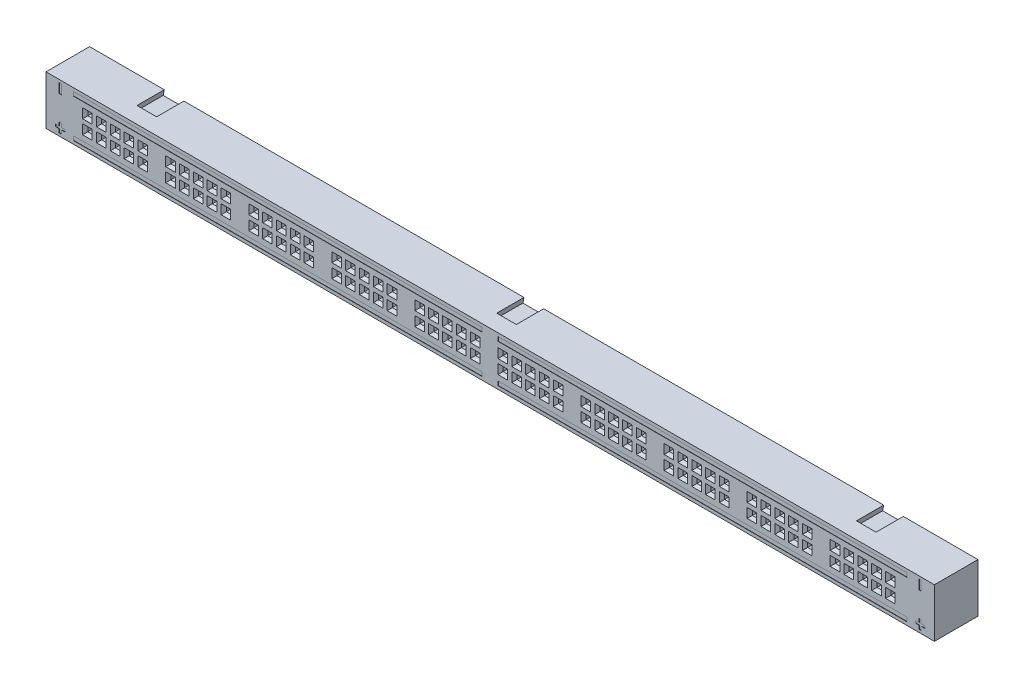
SolidWorks part; units mm, degrees
ref_plane "Front Plane" through (0, 0, 0) normal (0, 0, 1) x (1, 0, 0)
ref_plane "Top Plane" through (0, 0, 0) normal (0, 1, 0) x (1, 0, 0)
ref_plane "Right Plane" through (0, 0, 0) normal (1, 0, 0) x (0, 0, -1)
sketch "Sketch1" plane through (0, 0, 0) normal (0, 0, 1) x (1, 0, 0)
  line L1 (0, 0) -> (163, 0)
  line L2 (0, 0) -> (0, 9)
  line L3 (0, 9) -> (163, 9)
  line L4 (163, 0) -> (163, 9)
  dimension "D1" = 163
  dimension "D2" = 9
extrude "Boss-Extrude1" add sketch "Sketch1" along normal blind 8
sketch "Sketch2" plane through (0, 0, 8) normal (0, 0, 1) x (1, 0, 0)
  line L0 (163, 0) -> (163, 9) construction
  line L1 (163, 0) -> (163, 9)
  line L2 (154.92, 0) -> (154.92, 9) construction
  line L3 (154.92, 4.5) -> (159.3402, 4.5) construction
  line L5 (154.92, 5.77) -> (159.3402, 5.77) construction
  line L6 (154.045, 6.645) -> (155.795, 6.645)
  line L7 (154.045, 6.645) -> (154.045, 4.895)
  line L8 (154.045, 4.895) -> (155.795, 4.895)
  line L9 (155.795, 6.645) -> (155.795, 4.895)
  line L10 (154.045, 6.645) -> (155.795, 4.895) construction
  line L11 (154.045, 4.895) -> (155.795, 6.645) construction
  line L16 (154.52, 5.37) -> (155.32, 6.17) construction
  line L17 (154.52, 6.17) -> (155.32, 5.37) construction
  dimension "D2" = 1.75
  dimension "D1" = 8.08
  dimension "D3" = 1.27
extrude "Cut-Extrude1" cut sketch "Sketch2" against normal blind 8 draft 45 contours L9 L6 L7 L8
sketch "Sketch3" plane through (0, 0, 8) normal (0, 0, 1) x (1, 0, 0)
  line L0 (154.045, 4.895) -> (155.795, 6.645) construction
  line L2 (154.52, 5.37) -> (155.32, 5.37)
  line L3 (154.52, 5.37) -> (154.52, 6.17)
  line L4 (154.52, 6.17) -> (155.32, 6.17)
  line L5 (155.32, 5.37) -> (155.32, 6.17)
  line L6 (154.52, 5.37) -> (155.32, 6.17) construction
  line L7 (154.52, 6.17) -> (155.32, 5.37) construction
  point P4 (154.92, 5.77)
extrude "Cut-Extrude2" cut sketch "Sketch3" against normal blind 5
ref_plane "Plane1" through (0, 4.5, 0) normal (0, -1, 0) x (-1, 0, 0)
mirror "Mirror1" about plane through (0, 4.5, 0) normal (0, -1, 0) of "Cut-Extrude2", "Cut-Extrude1"
pattern_linear "LPattern1" count 5 spacing 2.54 along (-1, 0, 0) of "Cut-Extrude2", "Cut-Extrude1", "Mirror1"
pattern_linear "LPattern2" count 10 spacing 15.24 along (-1, 0, 0) of "LPattern1", "Cut-Extrude1", "Cut-Extrude2", "Mirror1"
sketch "Sketch4" plane through (0, 0, 8) normal (0, 0, 1) x (1, 0, 0)
  line L0 (0, 0) -> (163, 0) construction
  line L1 (80.0399, 1.35) -> (5.0399, 1.35)
  line L2 (80.0399, 1.35) -> (80.0399, 0.6)
  line L3 (80.0399, 0.6) -> (5.0399, 0.6)
  line L4 (5.0399, 1.35) -> (5.0399, 0.6)
  dimension "D1" = 75
  dimension "D2" = 0.75
  dimension "D3" = 0.6
extrude "Cut-Extrude3" cut sketch "Sketch4" against normal blind 0.05
mirror "Mirror2" about plane through (0, 4.5, 0) normal (0, -1, 0) of "Cut-Extrude3"
ref_plane "Plane2" through (81.5, 0, 0) normal (-1, 0, 0) x (0, 0, 1)
mirror "Mirror3" about plane through (81.5, 0, 0) normal (-1, 0, 0) of "Cut-Extrude3", "Mirror2"
sketch "Sketch5" plane through (0, 0, 0) normal (0, 0, -1) x (-1, 0, 0)
  line L0 (-81.5, 0) -> (-81.5, -1) construction
  line L1 (0, 0) -> (-163, 0) construction
  line L2 (-79.7, 0) -> (-83.3, 0)
  line L3 (-79.5, -1) -> (-83.5, -1)
  line L4 (-83.5, -1) -> (-83.3, 0)
  line L5 (-79.5, -1) -> (-79.7, 0)
  point P7 (-81.5, 0)
  point P10 (-81.5, -1)
  dimension "D1" = 1
  dimension "D2" = 4
  dimension "D3" = 3.6
extrude "Boss-Extrude2" add sketch "Sketch5" against normal blind 5
pattern_linear "LPattern3" count 2 spacing 66 along (-1, 0, 0) count 2 spacing 66 along (1, 0, 0) of "Boss-Extrude2"
sketch "Sketch6" plane through (0, 0, 0) normal (0, 0, -1) x (-1, 0, 0)
  line L0 (-15.5, -1) -> (-15.5, 9) construction
  line L1 (-17.5, -1) -> (-13.5, -1) construction
  line L2 (-163, 9) -> (0, 9) construction
  line L3 (-13.7, 9) -> (-17.3, 9)
  line L4 (-13.5, 8) -> (-17.5, 8)
  line L5 (-13.7, 9) -> (-13.5, 8)
  line L6 (-17.5, 8) -> (-17.3, 9)
  point P9 (-15.5, 9)
  point P12 (-15.5, 8)
  dimension "D1" = 1
extrude "Cut-Extrude4" cut sketch "Sketch6" against normal blind 5
pattern_linear "LPattern4" count 3 spacing 66 along (1, 0, 0) of "Cut-Extrude4"
sketch "Sketch7" plane through (0, 0, 8) normal (0, 0, 1) x (1, 0, 0)
  line L0 (2.425, 2.25) -> (2.825, 0.5) construction
  line L1 (2.425, 2.25) -> (2.825, 2.25)
  line L2 (2.425, 2.25) -> (2.425, 1.575)
  line L3 (2.425, 0.5) -> (2.825, 0.5)
  line L4 (2.825, 2.25) -> (2.825, 1.575)
  line L5 (2.825, 1.575) -> (3.5, 1.575)
  line L6 (1.75, 1.575) -> (2.425, 1.575)
  line L7 (1.75, 1.575) -> (1.75, 1.175)
  line L8 (1.75, 1.175) -> (2.425, 1.175)
  line L9 (3.5, 1.575) -> (3.5, 1.175)
  line L10 (1.75, 1.575) -> (3.5, 1.175) construction
  line L11 (1.75, 1.175) -> (3.5, 1.575) construction
  line L12 (2.425, 1.175) -> (2.425, 0.5)
  line L13 (0, 9) -> (0, 0) construction
  line L14 (2.825, 1.175) -> (3.5, 1.175)
  line L15 (2.825, 1.175) -> (2.825, 0.5)
  line L16 (0, 0) -> (163, 0) construction
  line L17 (0, 4.5) -> (4.9621, 4.5) construction
  line L22 (2.425, 6.75) -> (2.825, 6.75)
  line L23 (2.425, 8.5) -> (2.825, 8.5)
  line L24 (2.425, 8.5) -> (2.425, 6.75)
  line L25 (2.825, 8.5) -> (2.825, 6.75)
  point P4 (2.625, 1.375)
  dimension "D1" = 0.4
  dimension "D2" = 1.75
  dimension "D3" = 1.75
  dimension "D4" = 0.5
extrude "Cut-Extrude5" cut sketch "Sketch7" against normal blind 0.05
mirror "Mirror4" about plane through (81.5, 0, 0) normal (-1, 0, 0) of "Cut-Extrude5"
